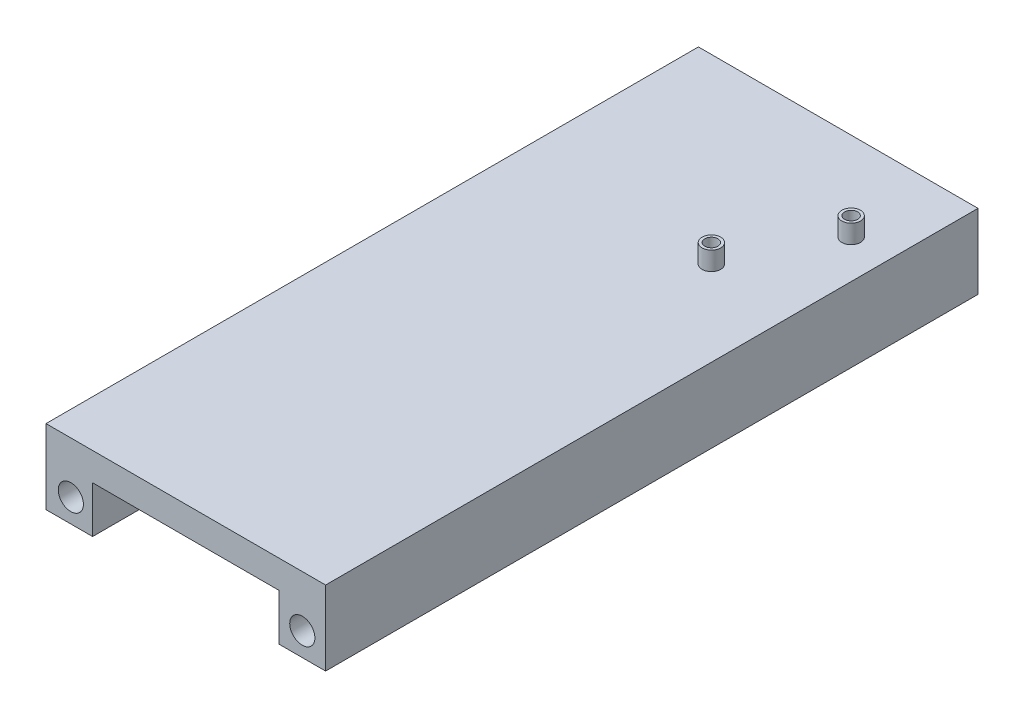
SolidWorks part; units mm, degrees
ref_plane "Front Plane" through (0, 0, 0) normal (0, 0, 1) x (1, 0, 0)
ref_plane "Top Plane" through (0, 0, 0) normal (0, 1, 0) x (1, 0, 0)
ref_plane "Right Plane" through (0, 0, 0) normal (1, 0, 0) x (0, 0, -1)
sketch "Sketch1" plane through (0, 0, 0) normal (0, 1, 0) x (1, 0, 0)
  line L1 (0, 0) -> (76.2, 0)
  line L2 (0, 0) -> (0, 177.8)
  line L3 (0, 177.8) -> (76.2, 177.8)
  line L4 (76.2, 0) -> (76.2, 177.8)
  dimension "D1" = 177.8
  dimension "D2" = 76.2
extrude "Boss-Extrude1" add sketch "Sketch1" along normal blind 7.62
sketch "Sketch4" plane through (0, 0, 0) normal (0, -1, 0) x (1, 0, 0)
  line L0 (76.2, -177.8) -> (0, -177.8) construction
  line L1 (0, 0) -> (12.7, 0)
  line L2 (0, 0) -> (0, -177.8)
  line L3 (0, -177.8) -> (12.7, -177.8)
  line L4 (12.7, 0) -> (12.7, -177.8)
  line L6 (76.2, 0) -> (63.5, 0)
  line L7 (76.2, 0) -> (76.2, -177.8)
  line L8 (76.2, -177.8) -> (63.5, -177.8)
  line L9 (63.5, 0) -> (63.5, -177.8)
  dimension "D1" = 12.7
  dimension "D2" = 12.7
extrude "Boss-Extrude2" add sketch "Sketch4" along normal blind 12.7
sketch "Sketch5" plane through (0, 0, -177.8) normal (0, 0, -1) x (-1, 0, 0)
  line L0 (-63.5, 0) -> (-76.2, 0) construction
  line L2 (-76.2, 7.62) -> (-76.2, -12.7) construction
  line L3 (-12.7, 0) -> (0, 0) construction
  line L4 (-76.2, 0) -> (-63.5, -12.7) construction
  line L5 (0, 0) -> (-13.5447, -12.7) construction
  line L6 (0, -12.7) -> (-12.7, -12.7) construction
  circle A0 centre (-69.85, -6.35) radius 3.429
  circle A1 centre (-6.7724, -6.35) radius 3.429
  dimension "D1" = 6.858
extrude "Cut-Extrude1" cut sketch "Sketch5" against normal through all
sketch "Sketch6" plane through (0, 7.62, 0) normal (0, 1, 0) x (1, 0, 0)
  line L0 (76.2, 0) -> (76.2, 177.8) construction
  line L1 (76.2, 177.8) -> (0, 177.8) construction
  circle A0 centre (65.7098, 153.7208) radius 1.778
  circle A1 centre (65.7098, 153.7208) radius 2.54
  circle A2 centre (53.0098, 128.3208) radius 1.778
  circle A3 centre (53.0098, 128.3208) radius 2.54
  point P6 (0, 0)
  point P7 (0, 0)
  point P8 (47.9662, 133.6211)
  dimension "D1" = 3.556
  dimension "D2" = 5.08
  dimension "D3" = 10.4902
  dimension "D4" = 24.0792
  dimension "D5" = 25.4
  dimension "D6" = 12.7
extrude "Boss-Extrude3" add sketch "Sketch6" along normal blind 5.08 contours A3 A2 | A1 A0
